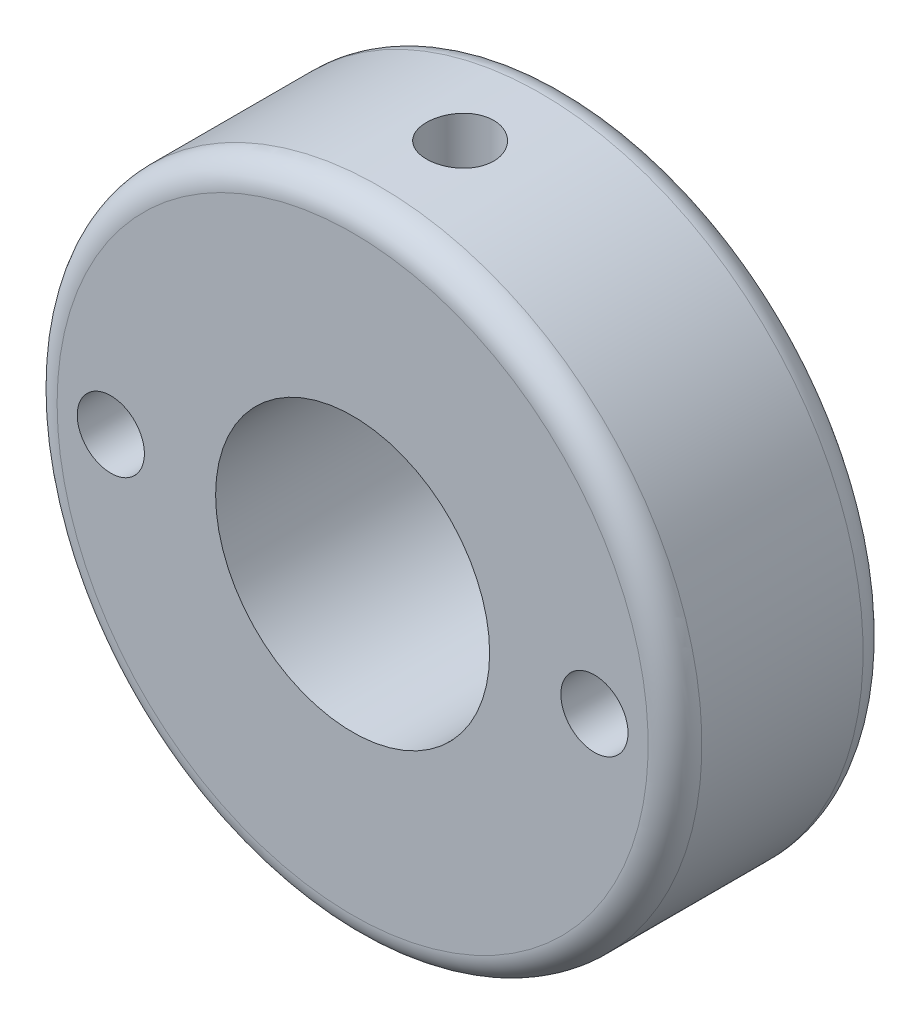
SolidWorks part; units mm, degrees
material "Malleable Cast Iron"
ref_plane "Front Plane" through (0, 0, 0) normal (0, 0, 1) x (1, 0, 0)
ref_plane "Top Plane" through (0, 0, 0) normal (0, 1, 0) x (1, 0, 0)
ref_plane "Right Plane" through (0, 0, 0) normal (1, 0, 0) x (0, 0, -1)
sketch "Sketch1" plane through (0, 0, 0) normal (0, 0, 1) x (1, 0, 0)
  line L1 (-12, -12) -> (12, -12)
  line L2 (-12, -12) -> (-12, 12)
  line L3 (-12, 12) -> (12, 12)
  line L4 (12, -12) -> (12, 12)
  line L5 (-12, -12) -> (12, 12) construction
  line L6 (-12, 12) -> (12, -12) construction
  point P0 (0, 0)
  dimension "D1" = 24
  dimension "D2" = 24
  dimension "D3" = 0
extrude "Boss-Extrude1" add sketch "Sketch1" along normal blind 8
hole_wizard "M3 Tapped Hole1" positions "Sketch6" profile "Sketch8" tap size "M3" standard "ISO" end condition through all
sketch "Sketch6" plane through (0, 0, 8) normal (0, 0, 1) x (1, 0, 0)
  point P0 (9, 0)
  point P2 (-9, 0)
  dimension "D1" = 9
  dimension "D2" = 9
cosmetic thread "Hole Thread2" parameters "D2"=3
cosmetic thread "Hole Thread3" parameters "D2"=3
sketch "Sketch8" plane through (9, 0, 8) normal (1, 0, 0) x (0, -1, 0)
  line L0 (0, 0) -> (0, 8)
  line L1 (0, 8) -> (1.25, 8)
  line L2 (1.25, 8) -> (1.25, 0)
  line L5 (1.25, 0) -> (0, 0)
  line L11 (0, -6.35) -> (0, 107.95) construction
  dimension "Thru Tap Drill Dia." = 2.5
  dimension "Thru Tap Drill Depth" = 8
hole_wizard "Ø10.2 (10.2) Diameter Hole1" positions "Sketch9" profile "Sketch11" hole size "Ø10.2" standard "ISO" end condition through all
sketch "Sketch9" plane through (0, 0, 0) normal (0, 0, -1) x (-1, 0, 0)
  point P0 (0, 0)
  dimension "D1" = 0
sketch "Sketch11" plane through (0, 0, 0) normal (1, 0, 0) x (0, 1, 0)
  line L0 (0, 0) -> (0, 8)
  line L1 (0, 8) -> (5.1, 8)
  line L2 (5.1, 8) -> (5.1, 0)
  line L5 (5.1, 0) -> (0, 0)
  line L11 (0, -6.35) -> (0, 107.95) construction
  dimension "Thru Hole Dia." = 10.2
  dimension "Thru Hole Depth" = 8
hole_wizard "M3 Tapped Hole2" positions "Sketch12" profile "Sketch14" tap size "M3" standard "ISO"
sketch "Sketch12" plane through (0, 12, 0) normal (0, 1, 0) x (1, 0, 0)
  line L0 (12, 0) -> (-12, 0) construction
  point P0 (0, -4)
  dimension "D1" = 4
sketch "Sketch14" plane through (0, 12, 4) normal (1, 0, 0) x (0, 0, 1)
  line L0 (0, 0) -> (0, 6.9)
  line L1 (0, 6.9) -> (1.25, 6.9)
  line L2 (1.25, 6.9) -> (1.25, 0)
  line L5 (1.25, 0) -> (0, 0)
  line L11 (0, -6.35) -> (0, 107.95) construction
  dimension "Thru Tap Drill Dia." = 2.5
  dimension "Thru Tap Drill Depth" = 6.9
cosmetic thread "Hole Thread4" parameters "D2"=3
sketch "Sketch15" plane through (0, 0, 0) normal (0, 0, -1) x (-1, 0, 0)
  circle A0 centre (0, 0) radius 12
  circle A3 centre (0, 0) radius 18.5
  dimension "D1" = 37
  dimension "D2" = 24
extrude "Cut-Extrude2" cut sketch "Sketch15" against normal blind 10 contours A3
fillet "Fillet2" radius 1 2 edges at (-12, 0, 0) (-12, 0, 8)
